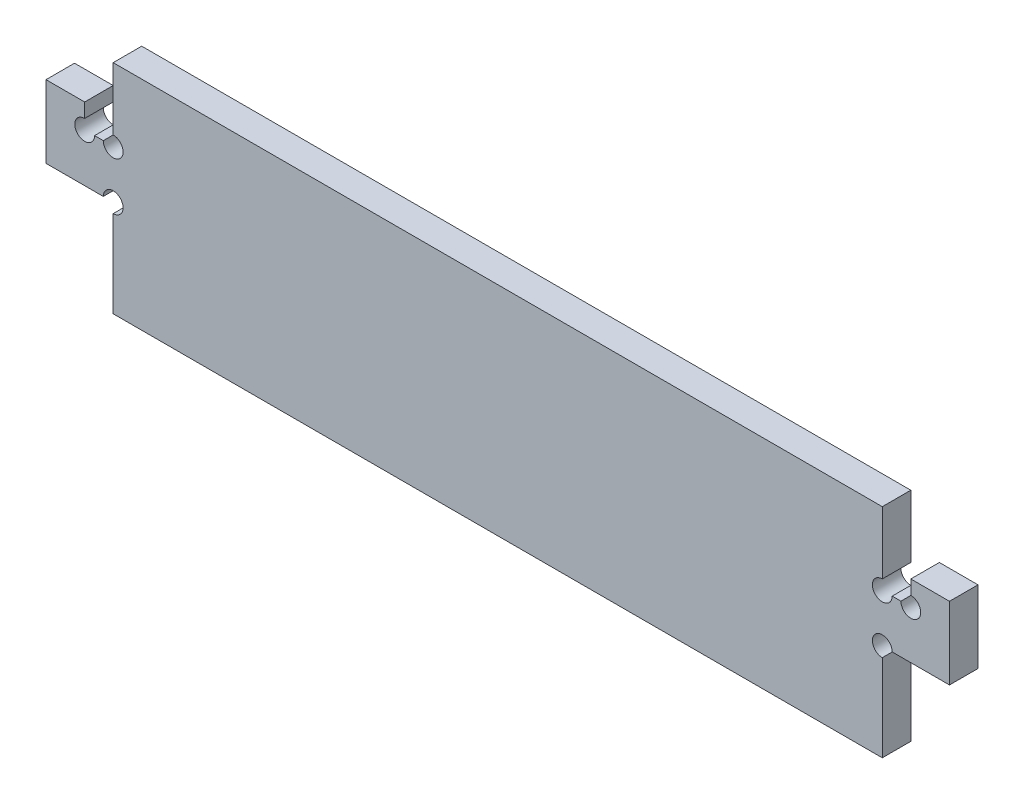
SolidWorks part; units mm, degrees
ref_plane "Front Plane" through (0, 0, 0) normal (0, 0, 1) x (1, 0, 0)
ref_plane "Top Plane" through (0, 0, 0) normal (0, 1, 0) x (1, 0, 0)
ref_plane "Right Plane" through (0, 0, 0) normal (1, 0, 0) x (0, 0, -1)
sketch "Sketch1" plane through (0, 0, 0) normal (0, 0, 1) x (1, 0, 0)
  line L1 (79.55, -22.5) -> (-79.55, -22.5)
  line L2 (79.55, -22.5) -> (79.55, 22.5)
  line L3 (79.55, 22.5) -> (-79.55, 22.5)
  line L4 (-79.55, -22.5) -> (-79.55, 22.5)
  line L5 (79.55, -22.5) -> (-79.55, 22.5) construction
  line L6 (79.55, 22.5) -> (-79.55, -22.5) construction
  point P0 (0, 0)
  dimension "D1" = 45
  dimension "D2" = 159.1
extrude "Boss-Extrude1" add sketch "Sketch1" along normal blind 5.9
sketch "Sketch3" plane through (0, 0, 5.9) normal (0, 0, 1) x (1, 0, 0)
  line L0 (-79.55, 7.5) -> (-85.45, 7.5)
  line L1 (-79.55, 22.5) -> (-79.55, -22.5) construction
  line L2 (-85.45, 7.5) -> (-85.45, 12.5)
  line L3 (-85.45, 12.5) -> (-93.45, 12.5)
  line L4 (-93.45, 12.5) -> (-93.45, -2.5)
  line L5 (-93.45, -2.5) -> (-85.45, -2.5)
  line L7 (-85.45, -2.5) -> (-79.55, -2.5)
  line L8 (-79.55, -2.5) -> (-79.55, 7.5)
  line L9 (79.55, 22.5) -> (-79.55, 22.5) construction
  line L10 (0, 0) -> (0, 23.0141) construction
  line L12 (79.55, -2.5) -> (79.55, 7.5)
  line L13 (85.45, -2.5) -> (79.55, -2.5)
  line L15 (93.45, -2.5) -> (85.45, -2.5)
  line L16 (93.45, 12.5) -> (93.45, -2.5)
  line L17 (85.45, 12.5) -> (93.45, 12.5)
  line L18 (85.45, 7.5) -> (85.45, 12.5)
  line L19 (79.55, 7.5) -> (85.45, 7.5)
  dimension "D1" = 10
  dimension "D2" = 15
  dimension "D4" = 8
  dimension "D5" = 5.9
  dimension "D3" = 15
extrude "Boss-Extrude3" add sketch "Sketch3" against normal up to surface (5.9 mm away) up to face at (0, 0, 0)
sketch "Sketch4" plane through (0, 0, 5.9) normal (0, 0, 1) x (1, 0, 0)
  circle A0 centre (-79.55, 7.5) radius 2.05
  circle A1 centre (-79.55, -2.5) radius 2.05
  circle A2 centre (79.55, -2.5) radius 2.05
  circle A3 centre (79.55, 7.5) radius 2.05
  circle A4 centre (-85.45, 7.5) radius 2.05
  circle A5 centre (85.45, 7.5) radius 2.05
  dimension "D1" = 4.1
extrude "Cut-Extrude1" cut sketch "Sketch4" against normal up to next
equation "\"e\" = 5.9"
equation "\"D1@Boss-Extrude1\"= \"e\""
equation "\"D5@Sketch3\"= \"e\""
equation "\"D2@Sketch1\"= 153.2 + \"e\""
